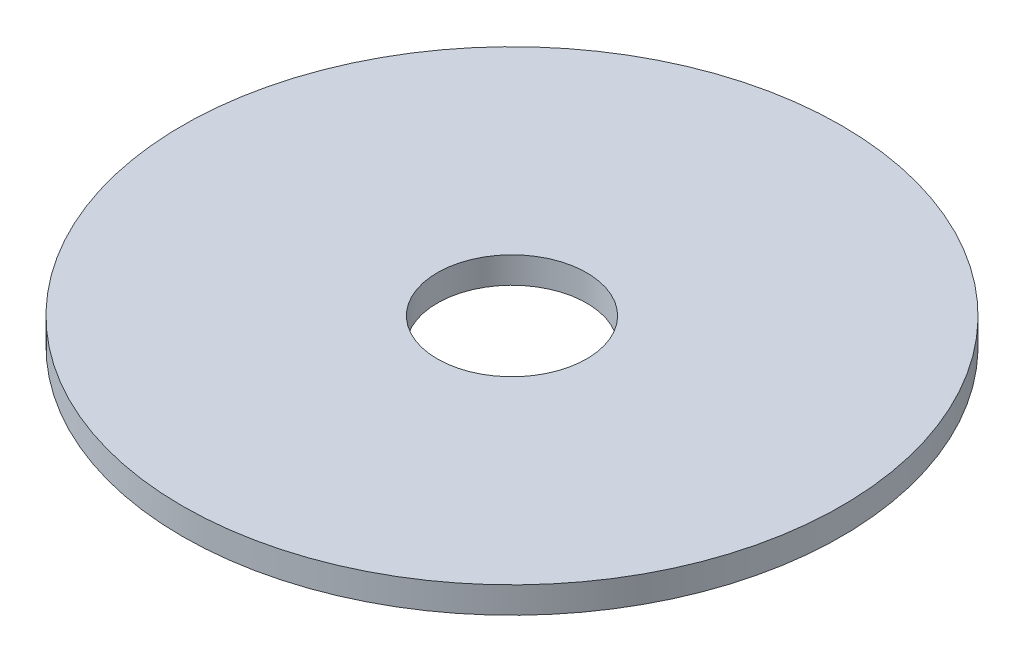
SolidWorks part; units mm, degrees
ref_plane "Front Plane" through (0, 0, 0) normal (0, 0, 1) x (1, 0, 0)
ref_plane "Top Plane" through (0, 0, 0) normal (0, 1, 0) x (1, 0, 0)
ref_plane "Right Plane" through (0, 0, 0) normal (1, 0, 0) x (0, 0, -1)
sketch "Sketch1" plane through (0, 0, 0) normal (0, 1, 0) x (1, 0, 0)
  circle A0 centre (0, 0) radius 2.159
  circle A1 centre (0, 0) radius 9.525
  dimension "D1" = 19.05
  dimension "D2" = 4.318
extrude "Boss-Extrude1" add sketch "Sketch1" along normal blind 0.762
